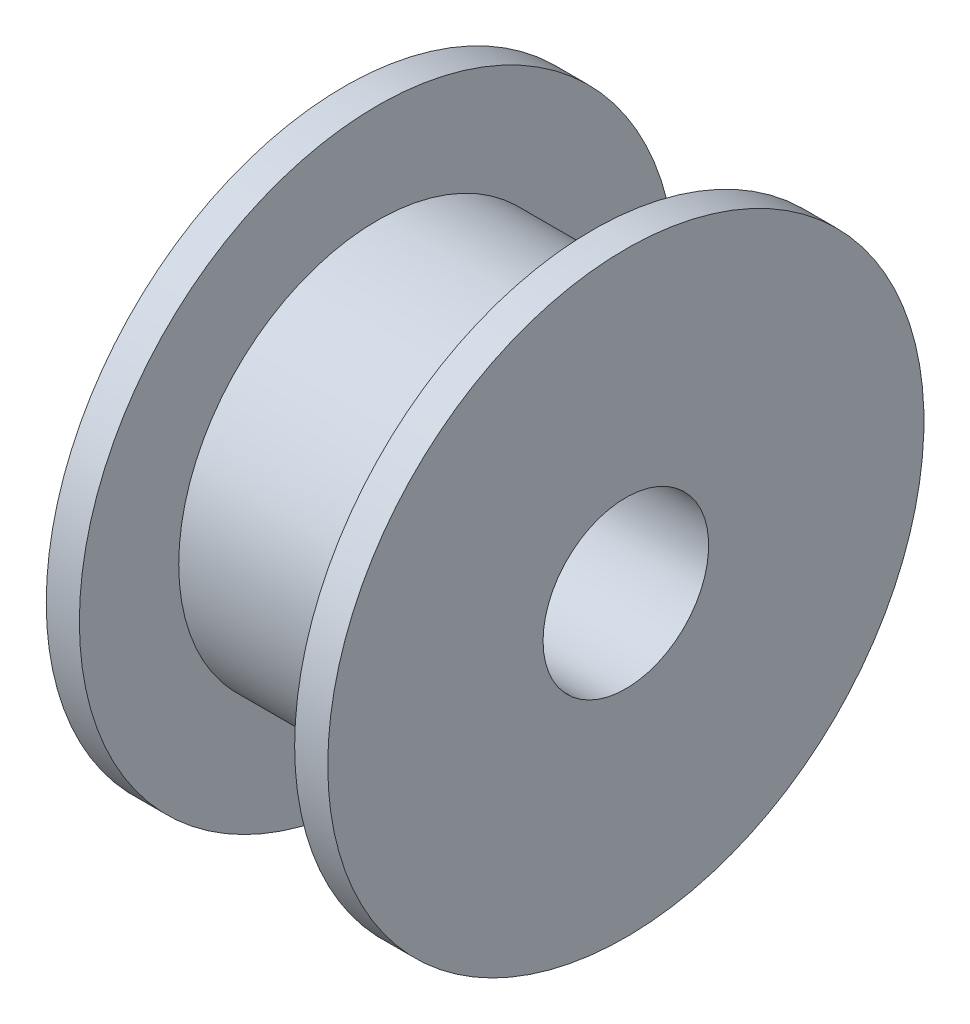
SolidWorks part; units mm, degrees
ref_plane "Front Plane" through (0, 0, 0) normal (0, 0, 1) x (1, 0, 0)
ref_plane "Top Plane" through (0, 0, 0) normal (0, 1, 0) x (1, 0, 0)
ref_plane "Right Plane" through (0, 0, 0) normal (1, 0, 0) x (0, 0, -1)
sketch "Sketch1" plane through (0, 0, 0) normal (0, 0, 1) x (1, 0, 0)
  line L0 (0, 0) -> (0, 9)
  line L1 (0, 9) -> (1, 9)
  line L2 (1, 9) -> (1, 6)
  line L3 (1, 6) -> (7.5, 6)
  line L4 (7.5, 6) -> (7.5, 9)
  line L5 (7.5, 9) -> (8.5, 9)
  line L6 (8.5, 9) -> (8.5, 0)
  line L7 (8.5, 0) -> (0, 0)
  line L8 (0, 0) -> (50, 0) construction
  point P5 (4.25, 6)
  point P11 (4.25, 0)
  dimension "D1" = 50
  dimension "D2" = 9
  dimension "D3" = 8.5
  dimension "D4" = 6.5
  dimension "D5" = 6
revolve "Revolve1" add sketch "Sketch1" angle 360 about L8
sketch "Sketch2" plane through (0, 0, 0) normal (-1, 0, 0) x (0, 0, 1)
  circle A0 centre (0, 0) radius 2.5
  dimension "D1" = 5
extrude "Cut-Extrude1" cut sketch "Sketch2" against normal through all
